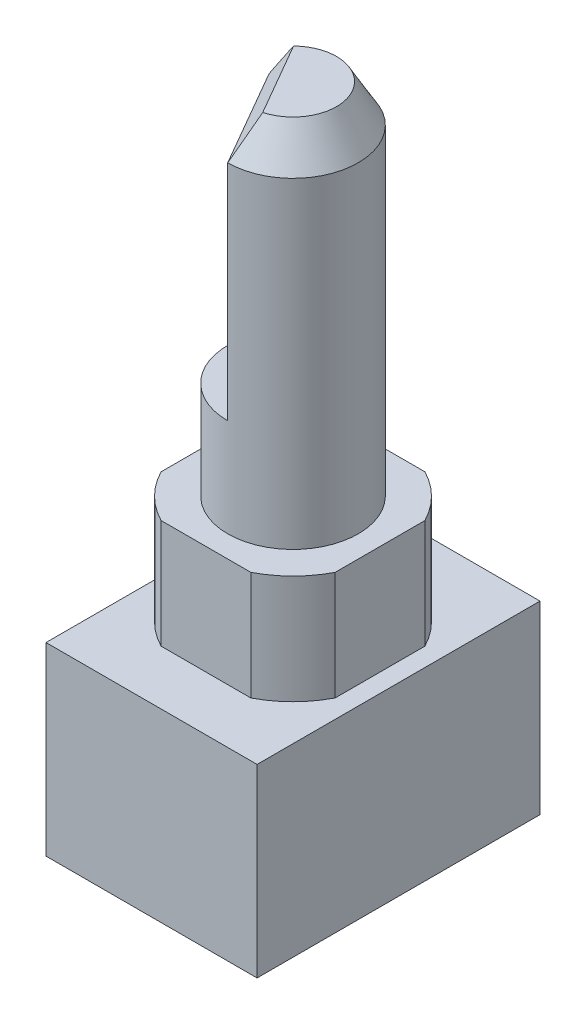
SolidWorks part; units mm, degrees
ref_plane "Front Plane" through (0, 0, 0) normal (0, 0, 1) x (1, 0, 0)
ref_plane "Top Plane" through (0, 0, 0) normal (0, 1, 0) x (1, 0, 0)
ref_plane "Right Plane" through (0, 0, 0) normal (1, 0, 0) x (0, 0, -1)
sketch "Sketch1" plane through (0, 0, 0) normal (0, 1, 0) x (1, 0, 0)
  line L1 (4.85, -6.5) -> (-4.85, -6.5)
  line L2 (4.85, -6.5) -> (4.85, 6.5)
  line L3 (4.85, 6.5) -> (-4.85, 6.5)
  line L4 (-4.85, -6.5) -> (-4.85, 6.5)
  line L5 (0, 6.5) -> (0, -6.5) construction
  line L6 (4.85, 0) -> (-4.85, 0) construction
  point P0 (0, 0)
  dimension "D1" = 9.7
  dimension "D2" = 13
extrude "Boss-Extrude1" add sketch "Sketch1" along normal blind 8.5
sketch "Sketch2" plane through (0, 8.5, 0) normal (0, 1, 0) x (1, 0, 0)
  circle A0 centre (0, 0) radius 4.5
  dimension "D1" = 9
extrude "Boss-Extrude2" add sketch "Sketch2" along normal blind 5
cosmetic thread "Cosmetic Thread1" parameters "D2"=6.619
sketch "Sketch3" plane through (0, 13.5, 0) normal (0, 1, 0) x (1, 0, 0)
  circle A0 centre (0, 0) radius 3
  dimension "D1" = 6
extrude "Boss-Extrude4" add sketch "Sketch3" along normal blind 21.5 from offset 5 offset against normal yes
sketch "Sketch4" plane through (0, 13.5, 0) normal (0, 1, 0) x (1, 0, 0)
  line L1 (4, -4) -> (-4, -4)
  line L2 (4, -4) -> (4, 4)
  line L3 (4, 4) -> (-4, 4)
  line L4 (-4, -4) -> (-4, 4)
  line L5 (0, 4) -> (0, -4) construction
  line L6 (4, 0) -> (-4, 0) construction
  circle A0 centre (0, 0) radius 4.5
  point P0 (0, 0)
  circle M4 centre (0, 0) radius 4.5
  dimension "D3" = 9
  dimension "D1" = 8
  dimension "D2" = 8
extrude "Cut-Extrude1" cut sketch "Sketch4" against normal up to surface (5 mm away) contours L4 M4 | L1 M4 | L2 M4 | L3 M4 up to face at (0, 8.5, 4.5)
sketch "Sketch5" plane through (0, 30, 0) normal (0, 1, 0) x (1, 0, 0)
  line L0 (0, 0) -> (0, 3) construction
  line L1 (0, -3) -> (-2.5981, 1.5)
  line L2 (-1.299, -0.75) -> (0, 0) construction
  circle A0 centre (0, 0) radius 3 construction
  circle A1 centre (0, 0) radius 3 construction
  arc A2 (0, -3) -> (-2.5981, 1.5) centre (0, 0) cw
  dimension "D1" = 1.5
  dimension "D2" = 120
extrude "Cut-Extrude2" cut sketch "Sketch5" against normal blind 12
chamfer "Chamfer1" distance 1 angle 60 2 edges at (2.5981, 30, -1.5) (-1.299, 30, 0.75)
